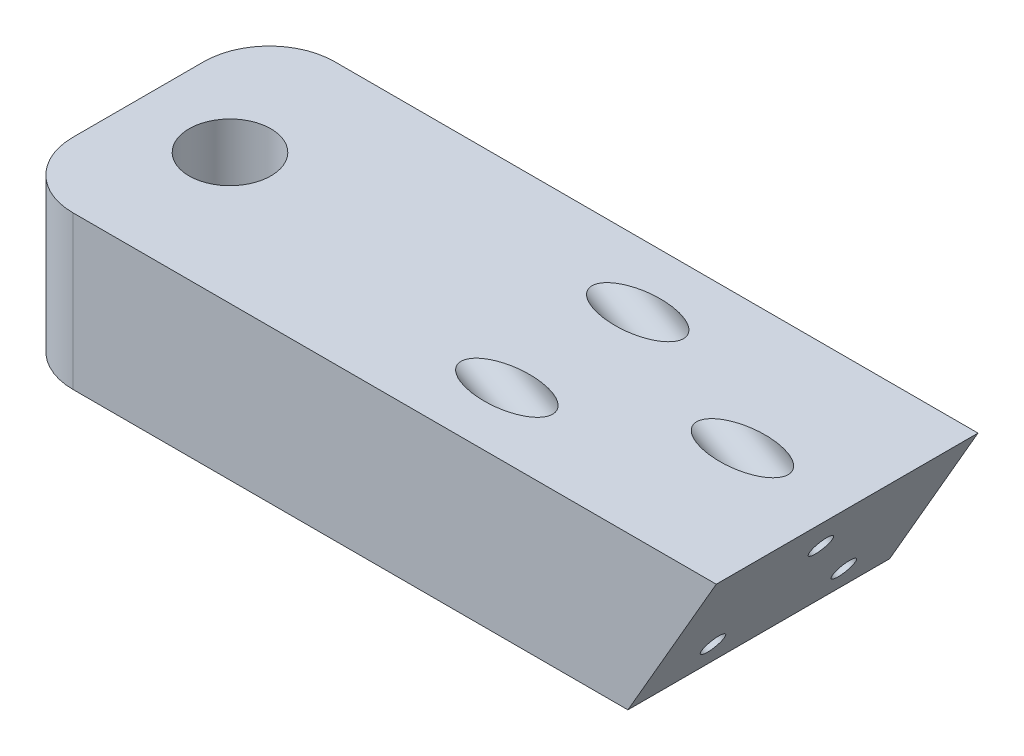
SolidWorks part; units mm, degrees
ref_plane "Alzado" through (0, 0, 0) normal (0, 0, 1) x (1, 0, 0)
ref_plane "Planta" through (0, 0, 0) normal (0, 1, 0) x (1, 0, 0)
ref_plane "Vista lateral" through (0, 0, 0) normal (1, 0, 0) x (0, 0, -1)
sketch "Croquis1" plane through (0, 0, 0) normal (0, 0, 1) x (1, 0, 0)
  line L0 (0, 0) -> (100, 0) construction
  line L1 (100, 0) -> (0, -173.2051) construction
  line L2 (0, -173.2051) -> (0, 0) construction
  line L3 (80.8135, 8.7679) -> (120.2176, -13.9821) construction
  line L4 (80.8135, 8.7679) -> (94.3135, 32.1506) construction
  line L5 (94.3135, 32.1506) -> (133.7176, 9.4006) construction
  line L6 (133.7176, 9.4006) -> (120.2176, -13.9821) construction
  line L7 (80.8135, 8.7679) -> (94.3135, 32.1506) construction
  line L8 (80.8135, 8.7679) -> (-13.9993, 8.7679)
  line L9 (-13.9993, 8.7679) -> (-13.9993, 32.1506)
  line L10 (-13.9993, 32.1506) -> (94.3135, 32.1506)
  line L11 (94.3135, 32.1506) -> (80.8135, 8.7679)
  line L12 (80.8135, 8.7679) -> (0, 8.7679) construction
  line L13 (100, 0) -> (96.1, -6.755) construction
  line L14 (96.1, -6.755) -> (0, -6.755) construction
  line L15 (0, 0) -> (0, 139.5928) construction
  line L16 (100, 0) -> (0, 57.735) construction
  line L17 (100, 0) -> (99.0491, 0.549) construction
  point P7 (100, 0)
  point P8 (100, 0)
  dimension "D1" = 100
  dimension "D2" = 30
  dimension "D3" = 90
  dimension "D4" = 30
  dimension "D5" = 200
  dimension "D6" = 27
  dimension "D7" = 45.5
  dimension "D8" = 21
  dimension "D9" = 108.3128
  dimension "D10" = 2
  dimension "D11" = 7.8
  dimension "D12" = 96.1
  dimension "D13" = 166.4501
  dimension "D14" = 1.098
  dimension "D15" = 114.3721
  dimension "D16" = 230.9401
extrude "Saliente-Extruir1" add sketch "Croquis1" along normal blind 40
sketch "Croquis2" plane through (0, 32.1506, 0) normal (0, 1, 0) x (1, 0, 0)
  line L0 (94.3135, 0) -> (-13.9993, 0) construction
  circle A0 centre (0, -20) radius 6.25
  dimension "D3" = 12.5
  dimension "D1" = 20
  dimension "D2" = 0
extrude "Cortar-Extruir1" cut sketch "Croquis2" against normal up to next
fillet "Redondeo1" radius 10 2 edges at (-13.9993, 20.4593, 40) (-13.9993, 20.4593, 0)
sketch "Croquis3" plane through (-13.9993, 0, 0) normal (-1, 0, 0) x (0, 0, 1)
  line L0 (30, 32.1506) -> (10, 32.1506) construction
  circle A0 centre (20, 20.1506) radius 2.3
  point P6 (20, 32.1506)
  dimension "D1" = 4.6
  dimension "D2" = 12
  dimension "D3" = 0
extrude "Cortar-Extruir2" cut sketch "Croquis3" against normal up to next
sketch "Croquis4" plane through (56.8135, -32.8013, 0) normal (0.866, -0.5, 0) x (0, 0, -1)
  line L0 (-40, 48) -> (0, 48) construction
  circle A0 centre (-30, 54) radius 1.75
  circle A1 centre (-10, 54) radius 1.75
  circle A2 centre (-20, 67) radius 1.75
  point P8 (-20, 48)
  dimension "D1" = 3.5
  dimension "D2" = 3.5
  dimension "D3" = 3.5
  dimension "D4" = 6
  dimension "D5" = 6
  dimension "D6" = 20
  dimension "D7" = 10
  dimension "D8" = 13
  dimension "D9" = 10
extrude "Cortar-Extruir3" cut sketch "Croquis4" against normal up to next
ref_plane "Plano1" through (51.6173, -29.8013, 0) normal (0.866, -0.5, 0) x (0, 0, -1)
sketch "Croquis5" plane through (51.6173, -29.8013, 0) normal (0.866, -0.5, 0) x (0, 0, -1)
  circle A0 centre (-30, 54) radius 3.5
  circle A1 centre (-20, 67) radius 3.5
  circle A2 centre (-10, 54) radius 3.5
  dimension "D1" = 7
  dimension "D2" = 7
  dimension "D3" = 7
extrude "Cortar-Extruir4" cut sketch "Croquis5" against normal up to next
